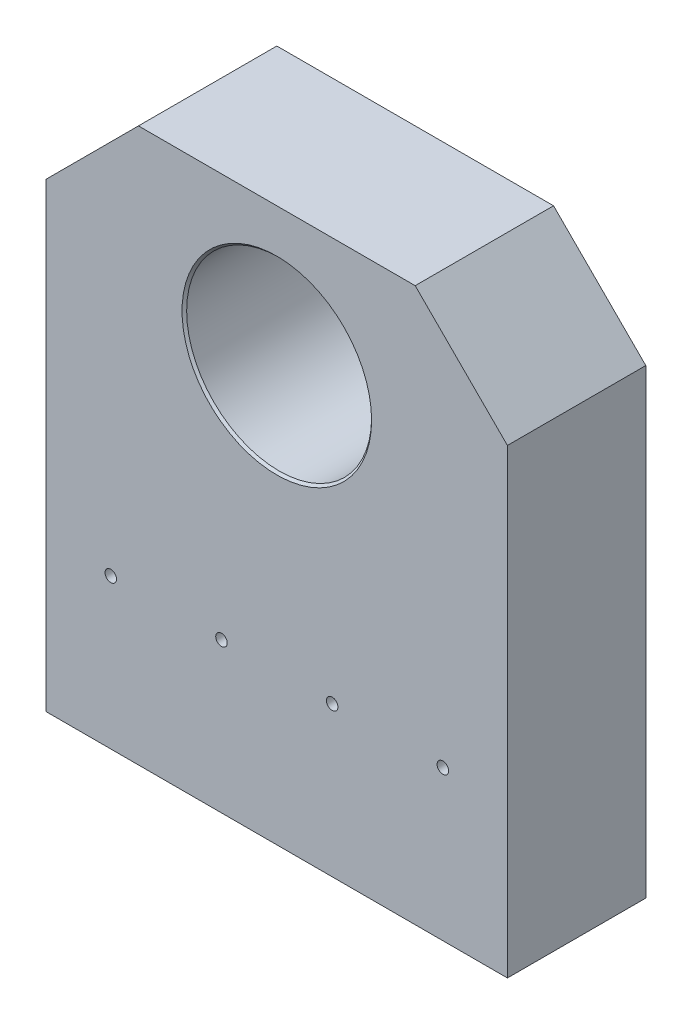
SolidWorks part; units mm, degrees
material "304 SSTL"
ref_plane "XY" through (0, 0, 0) normal (0, 0, 1) x (1, 0, 0)
ref_plane "XZ" through (0, 0, 0) normal (0, 1, 0) x (1, 0, 0)
ref_plane "YZ" through (0, 0, 0) normal (1, 0, 0) x (0, 0, -1)
sketch "Sketch1" plane through (0, 0, 0) normal (0, 0, 1) x (1, 0, 0)
  line L1 (0, 0) -> (127, 0)
  line L2 (0, 0) -> (0, 152.4)
  line L3 (0, 152.4) -> (127, 152.4)
  line L4 (127, 0) -> (127, 152.4)
  dimension "D1" = 152.4
  dimension "D2" = 127
extrude "Extrude1" add sketch "Sketch1" along normal blind 38.1
hole_wizard "1 (1) Diameter Hole1" positions "Sketch6" profile "Sketch5" hole size "1" standard "Ansi Inch" end condition through all
sketch "Sketch6" plane through (0, 0, 38.1) normal (0, 0, 1) x (1, 0, 0)
  line L0 (0, 0) -> (127, 0) construction
  line L1 (0, 152.4) -> (0, 0) construction
  point P0 (63.5, 114.3)
  dimension "D1" = 114.3
  dimension "D2" = 63.5
sketch "Sketch5" plane through (63.5, 114.3, 38.1) normal (1, 0, 0) x (0, -1, 0)
  line L0 (0, 0) -> (0, 38.1)
  line L1 (0, 38.1) -> (26.0985, 38.1)
  line L2 (25.4635, 37.465) -> (25.4635, 0.635)
  line L3 (25.4635, 0.635) -> (26.0985, 0)
  line L5 (26.0985, 0) -> (0, 0)
  line L6 (-25.4635, 0.635) -> (-26.0985, 0) construction
  line L7 (26.0985, 38.1) -> (25.4635, 37.465)
  line L8 (-26.0985, 38.1) -> (-25.4635, 37.465) construction
  line L11 (0, -6.35) -> (0, 107.95) construction
  dimension "Thru Hole Dia." = 50.927
  dimension "Thru Hole Depth" = 38.1
  dimension "Near C'Sink Dia." = 52.197
  dimension "Near C'Sink Angle" = 90
  dimension "Far C'Sink Dia." = 52.197
  dimension "Far C'Sink Angle" = 90
chamfer "Chamfer1" distance 25.4 angle 45 2 edges at (0, 152.4, 19.05) (127, 152.4, 19.05)
sketch "Sketch2" plane through (0, 0, 0) normal (0, -1, 0) x (1, 0, 0)
  line L0 (0, 25.4) -> (127, 25.4) construction
  line L3 (0, 38.1) -> (127, 38.1) construction
  line L4 (127, 38.1) -> (127, 0) construction
  line L5 (63.5, 38.1) -> (63.5, 0) construction
  line L6 (0, 0) -> (127, 0) construction
  circle A0 centre (109.22, 25.4) radius 5.3581 construction
  circle A1 centre (78.74, 25.4) radius 5.3581 construction
  circle A2 centre (48.26, 25.4) radius 5.3581 construction
  circle A3 centre (17.78, 25.4) radius 5.3581 construction
  dimension "D2" = 10.7163
  dimension "D3" = 30.48
  dimension "D4" = 17.78
  dimension "D1" = 12.7
hole_wizard "1/2-13 Tapped Hole1" positions "3DSketch1" profile "Sketch3" tap size "1/2-13" standard "Ansi Inch"
sketch3d "3DSketch1"
  point P0 (109.22, 0, 25.4)
  point P2 (78.74, 0, 25.4)
  point P4 (48.26, 0, 25.4)
  point P6 (17.78, 0, 25.4)
cosmetic thread "Cosmetic Thread1" parameters "D1"=31.75, "D2"=12.7
cosmetic thread "Cosmetic Thread2" parameters "D1"=31.75, "D2"=12.7
cosmetic thread "Cosmetic Thread3" parameters "D1"=31.75, "D2"=12.7
cosmetic thread "Cosmetic Thread4" parameters "D1"=31.75, "D2"=12.7
sketch "Sketch3" plane through (109.22, 0, 25.4) normal (1, 0, 0) x (0, 0, -1)
  line L0 (0, 0) -> (0, 47.6695)
  line L1 (0, 47.6695) -> (5.3581, 44.45)
  line L2 (5.3581, 44.45) -> (5.3581, 1.3729)
  line L3 (5.3581, 1.3729) -> (6.731, 0)
  line L5 (6.731, 0) -> (0, 0)
  line L6 (-5.3581, 1.3729) -> (-6.731, 0) construction
  line L10 (0, 47.6695) -> (-5.3581, 44.45) construction
  line L11 (0, -6.35) -> (0, 107.95) construction
  dimension "Tap Drill Dia." = 10.7163
  dimension "Tap Drill Depth" = 44.45
  dimension "Near C'Sink Dia." = 13.462
  dimension "Near C'Sink Angle" = 90
  dimension "Drill Angle" = 118
sketch "Sketch4" plane through (0, 0, 38.1) normal (0, 0, 1) x (1, 0, 0)
  line L0 (0, 0) -> (127, 0) construction
  circle A0 centre (17.78, 41.275) radius 1.5875
  circle A1 centre (48.26, 41.275) radius 1.5875
  circle A2 centre (78.74, 41.275) radius 1.5875
  circle A3 centre (109.22, 41.275) radius 1.5875
  dimension "D2" = 3.175
  dimension "D1" = 41.275
extrude "Cut-Extrude1" cut sketch "Sketch4" against normal through all
